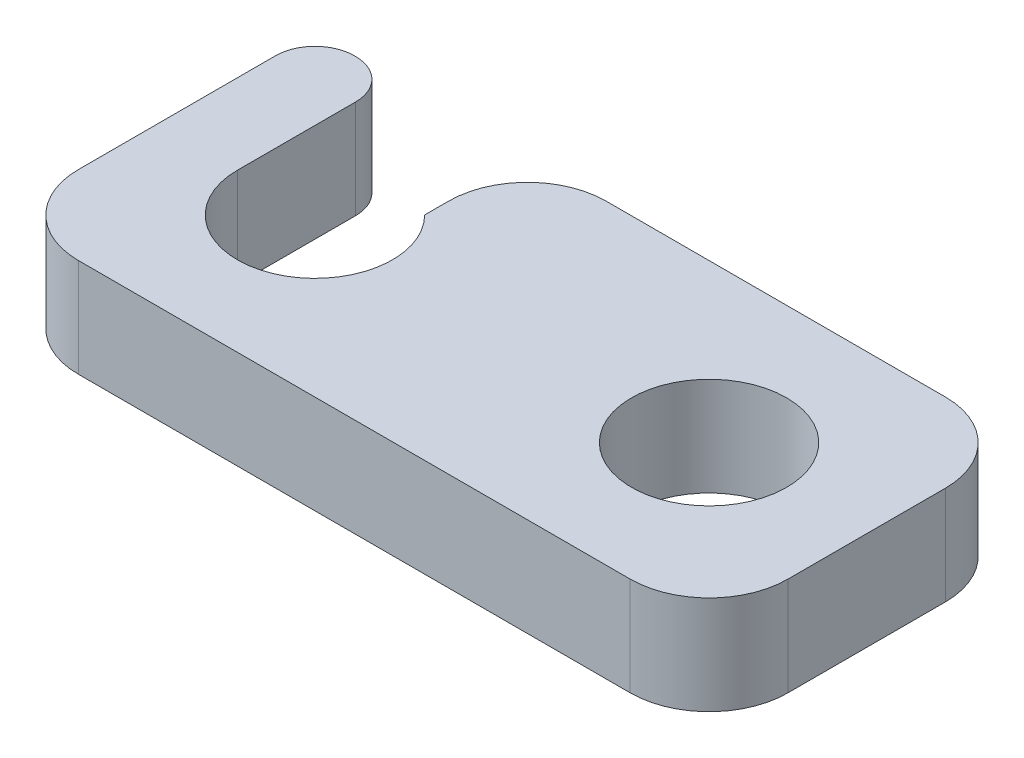
SolidWorks part; units mm, degrees
ref_plane "Front Plane" through (0, 0, 0) normal (0, 0, 1) x (1, 0, 0)
ref_plane "Top Plane" through (0, 0, 0) normal (0, 1, 0) x (1, 0, 0)
ref_plane "Right Plane" through (0, 0, 0) normal (1, 0, 0) x (0, 0, -1)
sketch "Sketch1" plane through (0, 0, 0) normal (0, 1, 0) x (1, 0, 0)
  line L1 (-11.43, -5.08) -> (11.43, -5.08)
  line L2 (-11.43, -5.08) -> (-11.43, 5.08)
  line L3 (-11.43, 5.08) -> (11.43, 5.08)
  line L4 (11.43, -5.08) -> (11.43, 5.08)
  line L5 (-11.43, -5.08) -> (11.43, 5.08) construction
  line L6 (-11.43, 5.08) -> (11.43, -5.08) construction
  point P0 (0, 0)
  dimension "D1" = 10.16
  dimension "D2" = 22.86
extrude "Boss-Extrude1" add sketch "Sketch1" along normal blind 3.175
sketch "Sketch2" plane through (0, 3.175, 0) normal (0, 1, 0) x (1, 0, 0)
  line L0 (11.43, 5.08) -> (-11.43, 5.08) construction
  line L1 (-11.43, 5.08) -> (-11.43, -5.08) construction
  line L2 (0, -5.08) -> (0, 5.08) construction
  line L3 (-11.43, -5.08) -> (11.43, -5.08) construction
  line L4 (-11.43, 0) -> (11.43, 0) construction
  line L5 (11.43, -5.08) -> (11.43, 5.08) construction
  circle A0 centre (-6.35, 0) radius 2.5
  circle A3 centre (6.35, 0) radius 2.5
  point P2 (-8.85, 0)
  point P3 (-6.35, 2.5)
  dimension "D1" = 5
  dimension "D2" = 12.7
extrude "Cut-Extrude1" cut sketch "Sketch2" against normal through all
sketch "Sketch3" plane through (0, 3.175, 0) normal (0, 1, 0) x (1, 0, 0)
  line L0 (-8.85, 0) -> (-8.85, 5.08)
  line L5 (-11.43, 5.08) -> (11.43, 5.08) construction
  line L6 (-8.85, 5.08) -> (-4.5845, 5.08)
  line L7 (-4.5845, 5.08) -> (-4.5845, 1.7701)
  circle A0 centre (-6.35, 0) radius 2.5 construction
  arc A1 (-4.5845, 1.7701) -> (-8.85, 0) centre (-6.35, 0) ccw
  dimension "D1" = 5.08
  dimension "D2" = 3.3099
extrude "Cut-Extrude2" cut sketch "Sketch3" against normal through all
fillet "Fillet1" radius 2.54 4 edges at (-11.43, 1.5875, 5.08) (-4.5845, 1.5875, -5.08) (11.43, 1.5875, 5.08) (11.43, 1.5875, -5.08)
fillet "Fillet2" radius 1.27 2 edges at (-11.43, 1.5875, -5.08) (-8.85, 1.5875, -5.08)
